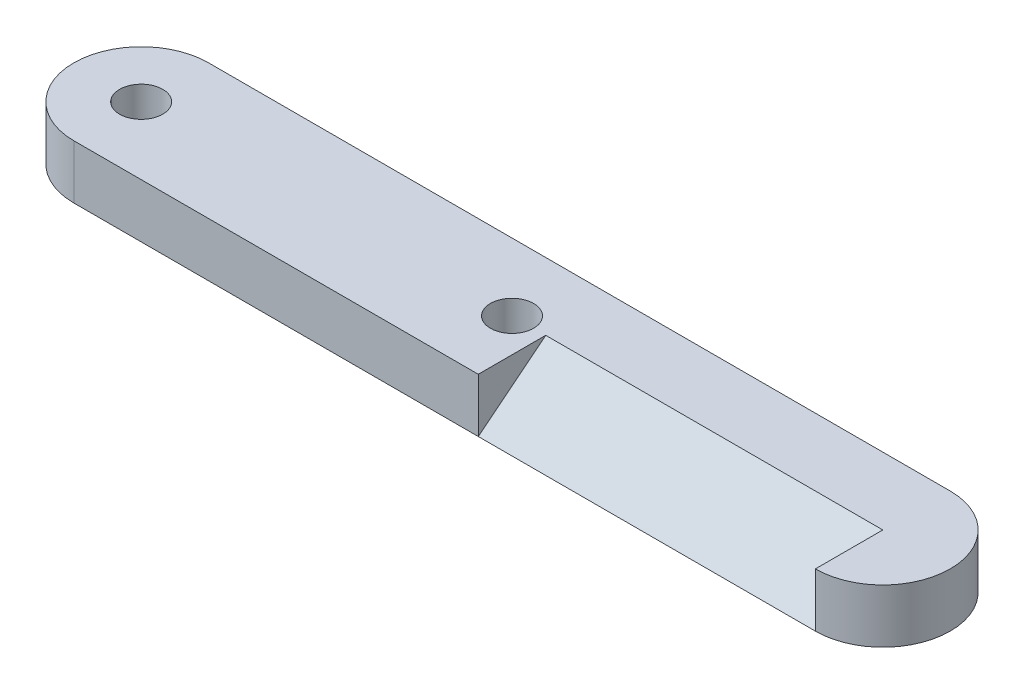
SolidWorks part; units mm, degrees
ref_plane "Front Plane" through (0, 0, 0) normal (0, 0, 1) x (1, 0, 0)
ref_plane "Top Plane" through (0, 0, 0) normal (0, 1, 0) x (1, 0, 0)
ref_plane "Right Plane" through (0, 0, 0) normal (1, 0, 0) x (0, 0, -1)
sketch "Sketch1" plane through (0, 0, 0) normal (0, 1, 0) x (1, 0, 0)
  line L0 (0, 0) -> (55, 0) construction
  line L1 (0, 5) -> (55, 5)
  line L2 (0, -5) -> (55, -5)
  arc A0 (0, 5) -> (0, -5) centre (0, 0) ccw
  arc A1 (55, -5) -> (55, 5) centre (55, 0) ccw
  point P3 (27.5, 0)
  dimension "D1" = 55
  dimension "D2" = 10
extrude "Boss-Extrude1" add sketch "Sketch1" along normal blind 4
sketch "Sketch2" plane through (0, 4, 0) normal (0, 1, 0) x (1, 0, 0)
  circle A0 centre (0, 0) radius 1.6
  circle A1 centre (27.5, 0) radius 1.6
  dimension "D1" = 3.2
  dimension "D2" = 3.2
  dimension "D3" = 27.5
extrude "Cut-Extrude1" cut sketch "Sketch2" against normal through all
sketch "Sketch5" plane through (0, 0, 5) normal (0, 0, 1) x (1, 0, 0)
  line L0 (0, 0) -> (55, 0) construction
  line L1 (55, 4) -> (30, 4)
  line L2 (55, 4) -> (55, 0)
  line L3 (55, 0) -> (30, 0)
  line L4 (30, 4) -> (30, 0)
  dimension "D1" = 25
extrude "Cut-Extrude2" cut sketch "Sketch5" against normal blind 5
sketch "Sketch6" plane through (30, 0, 0) normal (1, 0, 0) x (0, 0, -1)
  line L0 (0, 4) -> (-5, 0)
  line L1 (-5, 0) -> (0, 0)
  line L2 (0, 0) -> (0, 4)
extrude "Boss-Extrude3" add sketch "Sketch6" along normal blind 25
